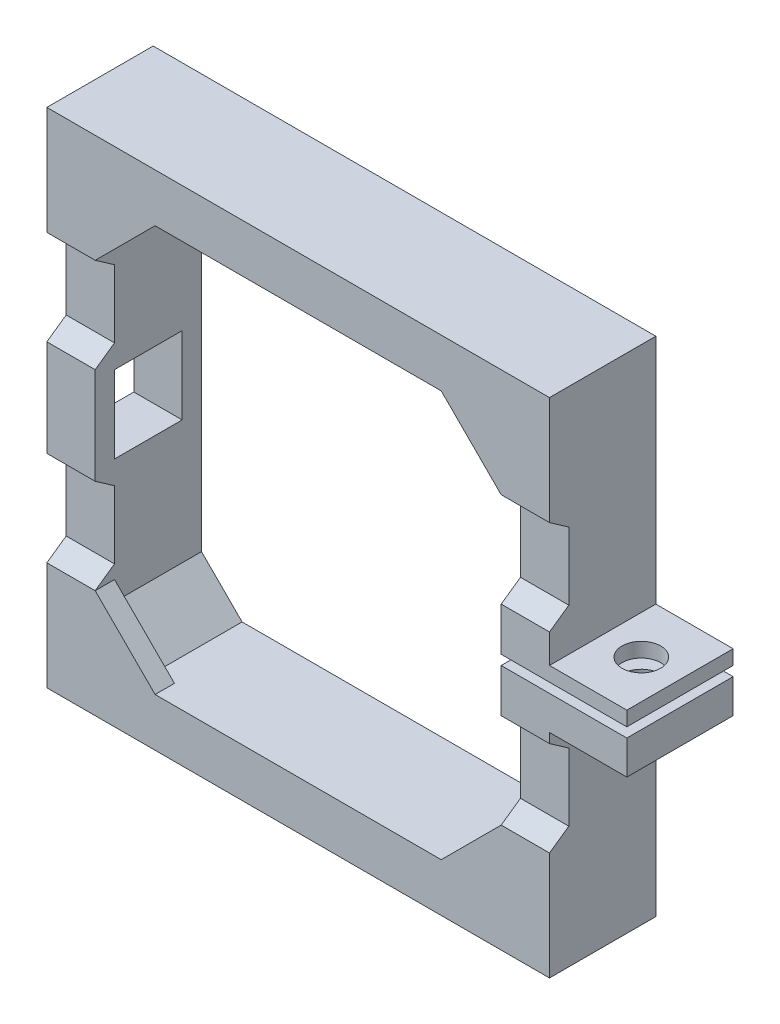
SolidWorks part; units mm, degrees
ref_plane "Plan de face" through (0, 0, 0) normal (0, 0, 1) x (1, 0, 0)
ref_plane "Plan de dessus" through (0, 0, 0) normal (0, 1, 0) x (1, 0, 0)
ref_plane "Plan de droite" through (0, 0, 0) normal (1, 0, 0) x (0, 0, -1)
sketch "Esquisse1" plane through (0, 0, 0) normal (0, 0, 1) x (1, 0, 0)
  line L1 (-21, 21) -> (21, 21)
  line L2 (-21, 21) -> (-21, -21)
  line L3 (-21, -21) -> (21, -21)
  line L4 (21, 21) -> (21, -21)
  line L5 (-21, 21) -> (21, -21) construction
  line L6 (-21, -21) -> (21, 21) construction
  line L7 (-26, 26) -> (26, 26)
  line L8 (-26, 26) -> (-26, -26)
  line L9 (-26, -26) -> (26, -26)
  line L10 (26, 26) -> (26, -26)
  line L11 (-26, 26) -> (26, -26) construction
  line L12 (-26, -26) -> (26, 26) construction
  point P0 (0, 0)
  point P6 (0, 0)
  dimension "D1" = 42
  dimension "D2" = 5
  dimension "D3" = 5
extrude "Boss.-Extru.1" add sketch "Esquisse1" along normal blind 11
sketch "Esquisse2" plane through (-26, 0, 0) normal (-1, 0, 0) x (0, 0, 1)
  line L0 (11, 14.8) -> (9, 13.4)
  line L1 (11, 26) -> (11, -26) construction
  line L2 (9, 13.4) -> (9, 6.4)
  line L3 (9, 6.4) -> (11, 5)
  line L4 (0, 26) -> (0, -26) construction
  line L5 (11, 14.8) -> (11, 5) construction
  line L6 (11, 9.9) -> (9, 9.9) construction
  dimension "D1" = 14.8
  dimension "D2" = 5
  dimension "D3" = 9
  dimension "D4" = 7
extrude "Enlèv. mat.-Extru.1" cut sketch "Esquisse2" against normal through all and the other way through all
mirror "Symétrie1" about plane through (0, 0, 0) normal (0, 1, 0) of "Enlèv. mat.-Extru.1"
sketch "Esquisse3" plane through (0, 0, 11) normal (0, 0, 1) x (1, 0, 0)
  line L0 (-21, 14.8) -> (-14.8, 21)
  line L1 (21, 21) -> (-21, 21) construction
  line L2 (-21, 21) -> (-21, 14.8) construction
  line L11 (-26, 26) -> (-26, 14.8)
  line L12 (-26, 14.8) -> (-21, 14.8)
  line L13 (-21, 14.8) -> (-21, 21)
  line L14 (-21, 21) -> (21, 21)
  line L15 (21, 21) -> (21, 14.8)
  line L16 (21, 14.8) -> (26, 14.8)
  line L17 (26, 14.8) -> (26, 26)
  line L18 (26, 26) -> (-26, 26)
  line L21 (-21, 14.8) -> (-21, 21)
  line L22 (-21, 21) -> (-14.8, 21)
  dimension "D1" = 45
  dimension "D2" = 0
extrude "Boss.-Extru.2" add sketch "Esquisse3" against normal blind 2
sketch "Esquisse6" plane through (0, 0, 9) normal (0, 0, -1) x (-1, 0, 0)
  line L0 (21, 21) -> (16.8, 21)
  line L2 (16.8, 21) -> (21, 16.8)
  line L4 (21, 16.8) -> (21, 21)
  line L5 (21, 21) -> (21, -21) construction
  line L7 (-21, 21) -> (21, 21) construction
  line L8 (21, 21) -> (21, 14.8) construction
  dimension "D1" = 4.2
  dimension "D2" = 45
extrude "Boss.-Extru.3" add sketch "Esquisse6" along normal blind 9
mirror "Symétrie2" about plane through (0, 0, 0) normal (1, 0, 0) of "Boss.-Extru.3", "Boss.-Extru.2"
mirror "Symétrie3" about plane through (0, 0, 0) normal (0, 1, 0) of "Symétrie2", "Boss.-Extru.2", "Boss.-Extru.3"
sketch "Esquisse4" plane through (-26, 0, 0) normal (-1, 0, 0) x (0, 0, 1)
  line L0 (0, 0) -> (5.5, 0) construction
  line L1 (2, 4) -> (9, 4)
  line L2 (2, 4) -> (2, -4)
  line L3 (2, -4) -> (9, -4)
  line L4 (9, 4) -> (9, -4)
  line L5 (2, 4) -> (9, -4) construction
  line L6 (2, -4) -> (9, 4) construction
  line L7 (9, 26) -> (9, -26) construction
  line L8 (11, 26) -> (0, 26) construction
  line L9 (11, -26) -> (0, -26) construction
  line L10 (0, 26) -> (0, -26) construction
  point P0 (5.5, 0)
  dimension "D1" = 8
  dimension "D2" = 7
  dimension "D3" = 9
extrude "Enlèv. mat.-Extru.2" cut sketch "Esquisse4" against normal up to next
sketch "Esquisse7" plane through (26, 0, 0) normal (1, 0, 0) x (0, 0, -1)
  line L0 (-11, 0) -> (0, 0) construction
  line L1 (-11, 2) -> (0, 2)
  line L2 (-11, 2) -> (-11, -4)
  line L3 (-11, -4) -> (0, -4)
  line L4 (0, 2) -> (0, -4)
  line L5 (-11, 2) -> (0, -4) construction
  line L6 (-11, -4) -> (0, 2) construction
  line L8 (-11, -5) -> (-11, 5) construction
  line L10 (0, -26) -> (0, 26) construction
  point P0 (-5.5, 0)
  dimension "D1" = 6
  dimension "D2" = 4
extrude "Boss.-Extru.4" add sketch "Esquisse7" along normal blind 8
sketch "Esquisse8" plane through (34, 0, 0) normal (1, 0, 0) x (0, 0, -1)
  line L0 (0, 0) -> (-11, 0) construction
  line L1 (-11, 0.5) -> (0, 0.5)
  line L2 (-11, 0.5) -> (-11, -0.5)
  line L3 (-11, -0.5) -> (0, -0.5)
  line L4 (0, 0.5) -> (0, -0.5)
  line L5 (-11, 0.5) -> (0, -0.5) construction
  line L6 (-11, -0.5) -> (0, 0.5) construction
  line L8 (0, -4) -> (0, 2) construction
  line L9 (-11, 2) -> (-11, -4) construction
  point P0 (-5.5, 0)
  dimension "D1" = 1
extrude "Enlèv. mat.-Extru.3" cut sketch "Esquisse8" against normal up to next
sketch "Esquisse9" plane through (0, -4, 0) normal (0, -1, 0) x (1, 0, 0)
  line L1 (33.4641, 5.5) -> (31.7321, 8.5)
  line L2 (31.7321, 8.5) -> (28.2679, 8.5)
  line L3 (28.2679, 8.5) -> (26.5359, 5.5)
  line L4 (26.5359, 5.5) -> (28.2679, 2.5)
  line L5 (28.2679, 2.5) -> (31.7321, 2.5)
  line L6 (31.7321, 2.5) -> (33.4641, 5.5)
  line L9 (34, 5.5) -> (26, 5.5) construction
  line L10 (34, 11) -> (34, 0) construction
  line L11 (26, 11) -> (26, 0) construction
  circle A0 centre (30, 5.5) radius 3 construction
  dimension "D1" = 6
extrude "Enlèv. mat.-Extru.4" cut sketch "Esquisse9" against normal blind 2.5
sketch "Esquisse10" plane through (0, -1.5, 0) normal (0, -1, 0) x (1, 0, 0)
  line L0 (26.5359, 5.5) -> (33.4641, 5.5) construction
  circle A0 centre (30, 5.5) radius 2
  dimension "D1" = 4
extrude "Enlèv. mat.-Extru.5" cut sketch "Esquisse10" against normal up to surface (3.5 mm away) up to face at (32, 2, 4.125)
